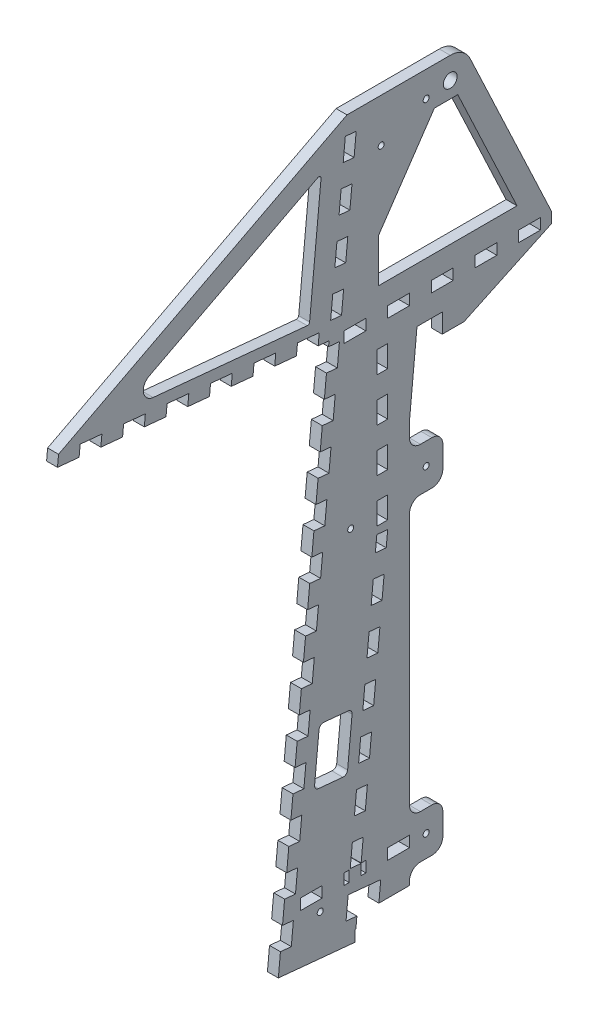
SolidWorks part; units mm, degrees
ref_plane "Front Plane" through (0, 0, 0) normal (0, 0, 1) x (1, 0, 0)
ref_plane "Top Plane" through (0, 0, 0) normal (0, 1, 0) x (1, 0, 0)
ref_plane "Right Plane" through (0, 0, 0) normal (1, 0, 0) x (0, 0, -1)
sketch "Sketch1" plane through (0, 0, 0) normal (1, 0, 0) x (0, 0, -1)
  line L0 (0, 0) -> (40.3547, 419.1) construction
  line L1 (40.3547, 419.1) -> (159.2585, 419.1) construction
  line L2 (159.2585, 419.1) -> (159.2585, 0) construction
  line L3 (159.2585, 0) -> (0, 0) construction
  line L4 (159.2585, -1000) -> (159.2585, 49000) construction
  line L5 (2.0164, 20.9415) -> (40.3547, 419.1) construction
  line L6 (2.0164, 20.9415) -> (41.8323, 17.1077) construction
  line L7 (40.3547, 419.1) -> (80.1706, 415.2662) construction
  line L8 (41.8323, 17.1077) -> (80.1706, 415.2662) construction
  line L9 (64.0085, -1000) -> (64.0085, 49000) construction
  line L10 (-42.7214, 317.5) -> (-118.5706, 324.8034) construction
  line L11 (-20.0013, 414.3375) -> (40.196, 414.3375) construction
  line L12 (-1162.1335, 304.8) -> (48837.8665, 304.8) construction
  line L13 (-120.1415, 292.1) -> (-43.9415, 292.1) construction
  line L14 (-118.5706, 324.8034) -> (-43.9415, 292.1) construction
  line L15 (-42.7214, 317.5) -> (-120.1415, 292.1) construction
  line L16 (40.196, 338.1375) -> (-20.0013, 338.1375) construction
  line L17 (-128.0517, 325.7164) -> (29.8985, 310.5075)
  line L18 (-128.0517, 325.7164) -> (-127.4431, 332.0371)
  line L19 (-127.4431, 332.0371) -> (40.3547, 419.1)
  line L20 (40.3547, 419.1) -> (108.4585, 419.1)
  line L21 (108.4585, 419.1) -> (108.4585, 0) construction
  line L22 (29.8985, 310.5075) -> (0.4102, 4.2603)
  line L23 (0.4102, 4.2603) -> (44.6556, 0)
  line L24 (44.6556, 0) -> (108.4585, 0)
  line L25 (108.4585, 419.1) -> (159.2585, 311.15)
  line L26 (159.2585, 311.15) -> (159.2585, 304.8)
  line L27 (159.2585, 304.8) -> (108.4585, 280.8941)
  line L28 (108.4585, 280.8941) -> (108.4585, 0)
  arc A0 (-118.5706, 324.8034) -> (-20.0013, 414.3375) centre (-20.0013, 315.3123) cw construction
  arc A1 (73.5335, 304.8) -> (40.196, 338.1375) centre (40.196, 304.8) ccw construction
  arc A2 (149.7335, 304.8) -> (40.196, 414.3375) centre (40.196, 304.8) ccw construction
  arc A3 (-42.7214, 317.5) -> (-20.0013, 338.1375) centre (-20.0013, 315.3123) cw construction
  point P7 (57.6585, 400.05)
  point P17 (149.7335, 304.8)
  point P18 (73.5335, 304.8)
  dimension "D9" = 9.525
  dimension "D14" = 25.4
  dimension "D1" = 419.1
  dimension "D2" = 101.6
  dimension "D3" = 19.05
  dimension "D4" = 19.05
  dimension "D5" = 84.5
  dimension "D6" = 40
  dimension "D7" = 400
  dimension "D8" = 95.25
  dimension "D10" = 9.525
  dimension "D11" = 114.3
  dimension "D12" = 76.2
  dimension "D13" = 9.525
  dimension "D15" = 127
  dimension "D16" = 9.525
  dimension "D17" = 203.2
  dimension "D18" = 6.35
  dimension "D19" = 50.8
  dimension "D20" = 44.45
  dimension "D21" = 6.35
extrude "Boss-Extrude1" add sketch "Sketch1" along normal blind 6.35
sketch "Sketch2" plane through (6.35, 0, 0) normal (1, 0, 0) x (0, 0, -1)
  line L0 (-93.8135, 335.1783) -> (25.4749, 397.0718)
  line L1 (25.4749, 397.0718) -> (18.4742, 324.3663)
  line L2 (18.4742, 324.3663) -> (-93.8135, 335.1783)
  line L3 (-128.0517, 325.7164) -> (29.8985, 310.5075) construction
  line L4 (-127.4431, 332.0371) -> (40.3547, 419.1) construction
  line L5 (29.8985, 310.5075) -> (0.4102, 4.2603) construction
  line L6 (91.1774, 397.0718) -> (84.127, 323.85)
  line L7 (81.0698, 292.1) -> (76.7085, 246.8069)
  line L8 (76.7085, 246.8069) -> (76.7085, 207.4333)
  line L9 (95.7585, 207.4333) -> (95.7585, 292.1)
  line L10 (95.7585, 292.1) -> (81.0698, 292.1)
  line L11 (95.7585, 194.7333) -> (95.7585, 110.0667)
  line L12 (95.7585, 97.3667) -> (95.7585, 12.7)
  line L13 (44.6556, 0) -> (108.4585, 0) construction
  line L14 (76.7085, 12.7) -> (76.7085, 97.3667)
  line L15 (76.7085, 97.3667) -> (95.7585, 97.3667)
  line L17 (95.7585, 12.7) -> (76.7085, 12.7)
  line L18 (64.0085, -201000) -> (64.0085, 249000) construction
  line L19 (84.127, 323.85) -> (139.2461, 323.85)
  line L20 (139.2461, 323.85) -> (104.7888, 397.0718)
  line L21 (104.7888, 397.0718) -> (91.1774, 397.0718)
  line L23 (108.4585, 419.1) -> (159.2585, 311.15) construction
  line L26 (41.8323, 17.1077) -> (80.1706, 415.2662) construction
  line L27 (95.7585, 110.0667) -> (76.7085, 110.0667)
  line L28 (-201162.1335, 304.8) -> (248837.8665, 304.8) construction
  line L29 (108.4585, 280.8941) -> (108.4585, 0) construction
  line L32 (76.7085, 110.0667) -> (76.7085, 194.7333)
  line L33 (76.7085, 194.7333) -> (95.7585, 194.7333)
  line L34 (76.7085, 207.4333) -> (95.7585, 207.4333)
  dimension "D1" = 12.7
  dimension "D2" = 12.7
  dimension "D3" = 12.7
  dimension "D5" = 12.7
  dimension "D6" = 12.7
  dimension "D7" = 12.7
  dimension "D8" = 12.7
  dimension "D9" = 12.7
  dimension "D10" = 12.7
  dimension "D11" = 12.7
  dimension "D12" = 12.7
  dimension "D13" = 12.7
extrude "Cut-Extrude4" cut sketch "Sketch2" against normal through all
fillet "Fillet1" radius 12.7 1 edges at (3.175, 419.1, -108.4585)
sketch "Sketch3" plane through (6.35, 0, 0) normal (1, 0, 0) x (0, 0, -1)
  circle A0 centre (100.3991, 406.4) radius 4
  dimension "D1" = 8
extrude "Cut-Extrude5" cut sketch "Sketch3" against normal through all
fillet "Fillet2" radius 6.35 1 edges at (3.175, 335.1783, 93.8135)
sketch "Sketch4" plane through (6.35, 0, 0) normal (1, 0, 0) x (0, 0, -1)
  line L0 (21.2562, 88.249) -> (24.3232, 120.1017)
  line L1 (21.2562, 88.249) -> (40.4673, 86.3992)
  line L2 (24.3232, 120.1017) -> (43.5344, 118.2519)
  line L3 (40.4673, 86.3992) -> (43.5344, 118.2519)
  line L4 (29.8985, 310.5075) -> (0.4102, 4.2603) construction
  line L5 (24.3232, 120.1017) -> (40.4673, 86.3992) construction
  line L6 (0.4102, 4.2603) -> (44.6556, 0) construction
  point P6 (32.3953, 103.2504)
  dimension "D1" = 101.6
  dimension "D2" = 32
  dimension "D3" = 12.7
  dimension "D4" = 32
extrude "Cut-Extrude6" cut sketch "Sketch4" against normal through all
sketch "Sketch5" plane through (6.35, 0, 0) normal (1, 0, 0) x (0, 0, -1)
  line L0 (1.6275, 16.9019) -> (2.8447, 29.5434)
  line L1 (1.6275, 16.9019) -> (7.9482, 16.2933)
  line L2 (2.8447, 29.5434) -> (9.1655, 28.9348)
  line L3 (7.9482, 16.2933) -> (9.1655, 28.9348)
  line L4 (29.8985, 310.5075) -> (0.4102, 4.2603) construction
  dimension "D1" = 12.7
  dimension "D2" = 12.7
  dimension "D3" = 6.35
extrude "Cut-Extrude11" cut sketch "Sketch5" against normal through all
pattern_linear "LPattern1" count 17 spacing 25.4 along (0, 0.9954, -0.0958) of "Cut-Extrude11"
sketch "Sketch7" plane through (6.35, 0, 0) normal (1, 0, 0) x (0, 0, -1)
  line L0 (23.5777, 311.1161) -> (10.9362, 312.3334)
  line L1 (23.5777, 311.1161) -> (24.1863, 317.4369)
  line L2 (10.9362, 312.3334) -> (11.5448, 318.6541)
  line L3 (24.1863, 317.4369) -> (11.5448, 318.6541)
  line L4 (-128.0517, 325.7164) -> (29.8985, 310.5075) construction
  line L5 (34.7275, 294.407) -> (35.9448, 307.0485) construction
  dimension "D1" = 12.7
  dimension "D2" = 12.7
  dimension "D3" = 6.35
extrude "Cut-Extrude13" cut sketch "Sketch7" against normal through all
pattern_linear "LPattern2" count 17 spacing 25.4 along (0, 0.0958, 0.9954) of "Cut-Extrude13"
sketch "Sketch8" plane through (6.35, 0, 0) normal (1, 0, 0) x (0, 0, -1)
  line L0 (159.2585, 304.8) -> (159.2585, 311.15) construction
  line L1 (152.9085, 311.15) -> (140.2085, 311.15)
  line L2 (152.9085, 311.15) -> (152.9085, 304.8)
  line L3 (152.9085, 304.8) -> (140.2085, 304.8)
  line L4 (140.2085, 311.15) -> (140.2085, 304.8)
  dimension "D1" = 6.35
  dimension "D2" = 12.7
extrude "Cut-Extrude14" cut sketch "Sketch8" against normal through all
pattern_linear "LPattern3" count 5 spacing 25.4 along (0, 0, 1) of "Cut-Extrude14"
sketch "Sketch9" plane through (6.35, 0, 0) normal (1, 0, 0) x (0, 0, -1)
  line L1 (108.4585, 0) -> (95.7585, 0)
  line L2 (108.4585, 0) -> (108.4585, 6.35)
  line L3 (108.4585, 6.35) -> (95.7585, 6.35)
  line L4 (95.7585, 0) -> (95.7585, 6.35)
  dimension "D1" = 12.7
  dimension "D2" = 6.35
extrude "Cut-Extrude15" cut sketch "Sketch9" against normal through all
pattern_linear "LPattern4" count 3 spacing 25.4 along (0, 0, 1) of "Cut-Extrude15"
sketch "Sketch11" plane through (6.35, 0, 0) normal (1, 0, 0) x (0, 0, -1)
  line L0 (39.8009, 13.2262) -> (46.1217, 12.6176)
  line L1 (39.8009, 13.2262) -> (41.0182, 25.8677)
  line L2 (46.1217, 12.6176) -> (47.3389, 25.2591)
  line L3 (41.0182, 25.8677) -> (47.3389, 25.2591)
  line L4 (0.4102, 4.2603) -> (44.6556, 0) construction
  line L5 (7.9482, 16.2933) -> (9.1655, 28.9348) construction
  line L6 (1.6275, 16.9019) -> (7.9482, 16.2933) construction
  line L7 (9.1655, 28.9348) -> (2.8447, 29.5434) construction
  dimension "D1" = 32
extrude "Cut-Extrude16" cut sketch "Sketch11" against normal through all
pattern_linear "LPattern5" count 8 spacing 25.4 along (0, 0.9954, -0.0958) of "Cut-Extrude16"
sketch "Sketch12" plane through (6.35, 0, 0) normal (1, 0, 0) x (0, 0, -1)
  line L0 (58.0595, 202.8492) -> (64.3803, 202.2405)
  line L1 (58.0595, 202.8492) -> (57.6878, 198.9884)
  line L2 (64.3803, 202.2405) -> (64.0085, 198.3798)
  line L3 (57.6878, 198.9884) -> (64.0085, 198.3798)
  line L4 (64.0085, -201000) -> (64.0085, 249000) construction
extrude "Boss-Extrude2" add sketch "Sketch12" against normal through all
sketch "Sketch13" plane through (6.35, 0, 0) normal (1, 0, 0) x (0, 0, -1)
  line L0 (76.7085, 97.3667) -> (76.7085, 12.7) construction
  line L1 (76.7085, 38.1) -> (64.0085, 38.1)
  line L2 (76.7085, 38.1) -> (76.7085, 31.75)
  line L3 (76.7085, 31.75) -> (64.0085, 31.75)
  line L4 (64.0085, 38.1) -> (64.0085, 31.75)
  line L5 (57.6585, 0) -> (70.3585, 0) construction
  dimension "D1" = 6.35
  dimension "D2" = 12.7
  dimension "D3" = 31.75
extrude "Cut-Extrude17" cut sketch "Sketch13" against normal through all
pattern_linear "LPattern6" count 3 spacing 25.4 along (0, 0, 1) skipping (1, 0) of "Cut-Extrude17"
sketch "Sketch15" plane through (6.35, 0, 0) normal (1, 0, 0) x (0, 0, -1)
  line L0 (25.9085, 38.1) -> (13.2085, 38.1) construction
  line L1 (38.6085, 38.1) -> (41.5845, 38.1)
  line L2 (38.6085, 38.1) -> (38.6085, 31.75)
  line L3 (38.6085, 31.75) -> (41.5845, 31.75)
  line L4 (41.5845, 38.1) -> (41.5845, 31.75)
  line L5 (51.3085, 31.75) -> (48.5754, 31.75) construction
  line L6 (51.3085, 31.75) -> (51.3085, 38.1) construction
  line L7 (51.3085, 38.1) -> (48.5754, 38.1) construction
  line L8 (48.5754, 31.75) -> (48.5754, 38.1) construction
  line L9 (13.2085, 31.75) -> (25.9085, 31.75) construction
  line L10 (25.9085, 31.75) -> (25.9085, 38.1) construction
  line L11 (64.0085, 38.1) -> (64.0085, 31.75) construction
  line L12 (43.4526, 51.1508) -> (42.2354, 38.5093) construction
  line L14 (48.5562, 37.9006) -> (49.7734, 50.5422) construction
  line L15 (48.5754, 31.75) -> (51.3085, 31.75)
  line L16 (51.3085, 31.75) -> (51.3085, 38.1)
  line L17 (51.3085, 38.1) -> (48.5754, 38.1)
  line L18 (48.5754, 38.1) -> (48.5562, 37.9006)
  line L19 (48.5562, 37.9006) -> (48.5754, 37.9006)
  line L20 (48.5754, 37.9006) -> (48.5754, 31.75)
  dimension "D1" = 12.7
  dimension "D2" = 12.7
extrude "Cut-Extrude20" cut sketch "Sketch15" against normal through all
sketch "Sketch16" plane through (6.35, 0, 0) normal (1, 0, 0) x (0, 0, -1)
  line L0 (47.3389, 25.2591) -> (45.5182, 6.35)
  line L1 (46.1217, 12.6176) -> (47.3389, 25.2591) construction
  line L2 (57.6585, 6.35) -> (44.9585, 6.35) construction
  line L3 (45.5182, 6.35) -> (58.2769, 6.35)
  line L4 (58.2769, 6.35) -> (59.9804, 24.0419)
  line L5 (59.9804, 24.0419) -> (47.3389, 25.2591)
  line L6 (47.3389, 25.2591) -> (41.0182, 25.8677) construction
  dimension "D1" = 12.7
extrude "Cut-Extrude21" cut sketch "Sketch16" against normal through all
sketch "Sketch17" plane through (6.35, 0, 0) normal (1, 0, 0) x (0, 0, -1)
  line L0 (76.7085, 311.15) -> (64.0085, 311.15) construction
  line L1 (64.0085, 304.8) -> (57.6585, 304.8)
  line L2 (64.0085, 304.8) -> (64.0085, 311.15)
  line L3 (64.0085, 311.15) -> (57.6585, 311.15)
  line L4 (57.6585, 304.8) -> (57.6585, 311.15)
extrude "Cut-Extrude22" cut sketch "Sketch17" against normal through all
sketch "Sketch18" plane through (6.35, 0, 0) normal (1, 0, 0) x (0, 0, -1)
  line L0 (57.6585, 311.15) -> (57.6585, 304.8) construction
  line L1 (57.6585, 292.1) -> (64.0085, 292.1)
  line L2 (57.6585, 292.1) -> (57.6585, 279.4)
  line L3 (57.6585, 279.4) -> (64.0085, 279.4)
  line L4 (64.0085, 292.1) -> (64.0085, 279.4)
  line L5 (51.3085, 304.8) -> (51.3085, 311.15) construction
  line L6 (38.6085, 304.8) -> (51.3085, 304.8) construction
  line L7 (57.6585, 304.8) -> (76.7085, 304.8) construction
  dimension "D1" = 12.7
extrude "Cut-Extrude23" cut sketch "Sketch18" against normal through all
pattern_linear "LPattern7" count 4 spacing 25.4 along (0, -1, 0) of "Cut-Extrude23"
sketch "Sketch19" plane through (6.35, 0, 0) normal (1, 0, 0) x (0, 0, -1)
  line L0 (59.0161, 381.0225) -> (-4733.2715, -49388.7875) construction
  line L1 (21.1033, 219.1664) -> (19.8861, 206.5249) construction
  line L2 (25.9723, 269.7325) -> (24.755, 257.091) construction
  line L3 (100.3991, 419.1) -> (40.3547, 419.1) construction
  circle A0 centre (42.5053, 209.5517) radius 1.75
  circle A1 centre (60.2368, 393.7) radius 1.75
  circle A2 centre (24.7739, 25.4034) radius 1.75
  dimension "D4" = 3.5
  dimension "D1" = 22.225
  dimension "D2" = 185
  dimension "D3" = 185
  dimension "D5" = 25.4
extrude "Cut-Extrude24" cut sketch "Sketch19" against normal through all
sketch "Sketch20" plane through (6.35, 0, 0) normal (1, 0, 0) x (0, 0, -1)
  line L0 (57.6585, 304.8) -> (76.7085, 304.8) construction
  line L1 (57.6585, 311.15) -> (64.0085, 311.15)
  line L2 (57.6585, 311.15) -> (57.6585, 304.8)
  line L3 (57.6585, 304.8) -> (64.0085, 304.8)
  line L4 (64.0085, 311.15) -> (64.0085, 304.8)
  line L5 (64.0085, 279.4) -> (64.0085, 292.1) construction
extrude "Boss-Extrude3" add sketch "Sketch20" against normal through all
fillet "Fillet3" radius 2.54 4 edges at (3.175, 118.2519, -43.5344) (3.175, 86.3992, -40.4673) (3.175, 88.249, -21.2562) (3.175, 120.1017, -24.3232)
fillet "Fillet4" radius 1.27 2 edges at (3.175, 324.3663, -18.4742) (3.175, 397.0718, -25.4749)
sketch "Sketch21" plane through (6.35, 0, 0) normal (1, 0, 0) x (0, 0, -1)
  line L0 (84.127, 323.85) -> (58.727, 323.85)
  line L1 (58.727, 323.85) -> (58.727, 349.25)
  line L2 (58.727, 349.25) -> (86.5727, 349.25)
  line L3 (91.1774, 397.0718) -> (84.127, 323.85) construction
  line L4 (86.5727, 349.25) -> (84.127, 323.85)
  dimension "D1" = 25.4
  dimension "D2" = 25.4
extrude "Cut-Extrude27" cut sketch "Sketch21" against normal through all contours L2 L4 L0 L1
sketch "Sketch22" plane through (6.35, 0, 0) normal (1, 0, 0) x (0, 0, -1)
  line L0 (58.727, 349.25) -> (91.1774, 397.0718)
  line L1 (91.1774, 397.0718) -> (86.5727, 349.25)
  line L2 (86.5727, 349.25) -> (58.727, 349.25)
extrude "Cut-Extrude28" cut sketch "Sketch22" against normal through all
sketch "Sketch23" plane through (6.35, 0, 0) normal (1, 0, 0) x (0, 0, -1)
  line L0 (108.4585, 6.35) -> (108.4585, 280.8941) construction
  line L1 (57.6585, 0) -> (108.4585, 0)
  line L2 (57.6585, 0) -> (57.6585, 12.7)
  line L3 (57.6585, 12.7) -> (108.4585, 12.7)
  line L4 (108.4585, 0) -> (108.4585, 12.7)
  line L5 (76.7085, 12.7) -> (95.7585, 12.7) construction
extrude "Cut-Extrude29" cut sketch "Sketch23" against normal through all
sketch "Sketch24" plane through (6.35, 0, 0) normal (1, 0, 0) x (0, 0, -1)
  line L0 (76.7085, 12.7) -> (76.7085, 207.4333)
  line L1 (108.4585, 280.8941) -> (76.7085, 280.8941) construction
  line L2 (108.4585, 280.8941) -> (108.4585, 12.7)
  line L3 (108.4585, 12.7) -> (76.7085, 12.7)
  line L4 (76.7085, 280.8941) -> (76.7085, 12.7) construction
  line L5 (76.7085, 207.4333) -> (95.7585, 280.8941)
  line L6 (95.7585, 207.4333) -> (95.7585, 292.1) construction
  line L7 (95.7585, 280.8941) -> (108.4585, 280.8941)
extrude "Cut-Extrude30" cut sketch "Sketch24" against normal through all
sketch "Sketch25" plane through (6.35, 0, 0) normal (1, 0, 0) x (0, 0, -1)
  line L0 (96.3991, -598.1261) -> (96.3991, 49401.8739) construction
  line L1 (100.3991, 419.1) -> (40.3547, 419.1) construction
  circle A0 centre (86.3991, 404.1) radius 1.75
  circle A2 centre (100.3991, 406.4) radius 4 construction
  circle A3 centre (60.2368, 393.7) radius 1.75 construction
  dimension "D1" = 10
  dimension "D2" = 15
extrude "Cut-Extrude32" cut sketch "Sketch25" against normal through all
sketch "Sketch26" plane through (0, 0, 0) normal (-1, 0, 0) x (0, 0, 1)
  line L0 (-76.7085, 239.6389) -> (-76.7085, 38.1) construction
  line L1 (-96.0896, 206.4) -> (-76.7085, 206.4)
  line L2 (-96.0896, 206.4) -> (-96.0896, 231.8)
  line L3 (-96.0896, 231.8) -> (-76.7085, 231.8)
  line L4 (-76.7085, 206.4) -> (-76.7085, 231.8)
  line L5 (-96.0896, 206.4) -> (-76.7085, 231.8) construction
  line L6 (-96.0896, 231.8) -> (-76.7085, 206.4) construction
  line L8 (-96.0896, 21.4) -> (-76.7085, 21.4)
  line L9 (-96.0896, 21.4) -> (-96.0896, 46.8)
  line L10 (-96.0896, 46.8) -> (-76.7085, 46.8)
  line L11 (-76.7085, 21.4) -> (-76.7085, 46.8)
  line L12 (-96.0896, 21.4) -> (-76.7085, 46.8) construction
  line L13 (-96.0896, 46.8) -> (-76.7085, 21.4) construction
  circle A0 centre (-86.3991, 219.1) radius 1.75
  circle A1 centre (-86.3991, 34.1) radius 1.75
  point P0 (-86.3991, 219.1)
  point P8 (-86.3991, 34.1)
  dimension "D3" = 3.5
  dimension "D1" = 25.4
  dimension "D2" = 25.4
extrude "Boss-Extrude4" add sketch "Sketch26" against normal blind 6.35
fillet "Fillet5" radius 6.35 8 edges at (3.175, 231.8, -76.7085) (3.175, 206.4, -76.7085) (3.175, 206.4, -96.0896) (3.175, 231.8, -96.0896) (3.175, 46.8, -76.7085) (3.175, 21.4, -76.7085) (3.175, 21.4, -96.0896) (3.175, 46.8, -96.0896)
